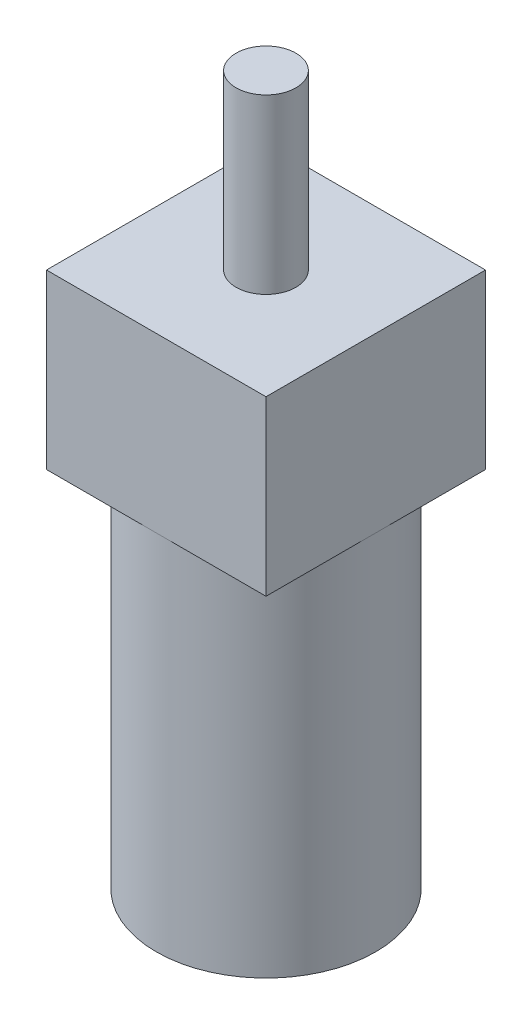
SolidWorks part; units mm, degrees
ref_plane "Front Plane" through (0, 0, 0) normal (0, 0, 1) x (1, 0, 0)
ref_plane "Top Plane" through (0, 0, 0) normal (0, 1, 0) x (1, 0, 0)
ref_plane "Right Plane" through (0, 0, 0) normal (1, 0, 0) x (0, 0, -1)
sketch "Sketch1" plane through (0, 0, 0) normal (0, 0, 1) x (1, 0, 0)
  line L0 (0, 10) -> (0, 22.7849) construction
  line L1 (-6.05, 10) -> (0, 10)
  line L2 (-6.05, 10) -> (-6.05, -10)
  line L3 (-6.05, -10) -> (0, -10)
  line L4 (0, 10) -> (0, -10)
  point P4 (0, 0)
  dimension "D1" = 20
  dimension "D2" = 12.1
revolve "Revolve1" add sketch "Sketch1" angle 360 about L4
sketch "Sketch2" plane through (0, 10, 0) normal (0, 1, 0) x (1, 0, 0)
  line L1 (6.05, -6.05) -> (-6.05, -6.05)
  line L2 (6.05, -6.05) -> (6.05, 6.05)
  line L3 (6.05, 6.05) -> (-6.05, 6.05)
  line L4 (-6.05, -6.05) -> (-6.05, 6.05)
  line L5 (6.05, -6.05) -> (-6.05, 6.05) construction
  line L6 (6.05, 6.05) -> (-6.05, -6.05) construction
  circle A0 centre (0, 0) radius 6.05 construction
  point P0 (0, 0)
extrude "Boss-Extrude1" add sketch "Sketch2" along normal blind 9.525
sketch "Sketch3" plane through (0, 19.525, 0) normal (0, 1, 0) x (1, 0, 0)
  circle A0 centre (0, 0) radius 1.6529
extrude "Boss-Extrude2" add sketch "Sketch3" along normal blind 9.525
